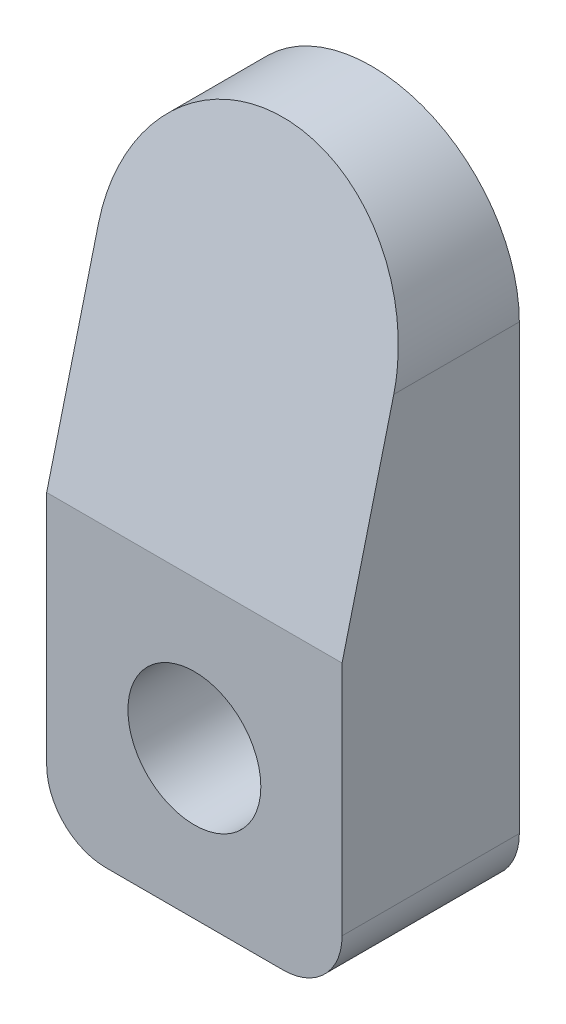
SolidWorks part; units mm, degrees
ref_plane "Front Plane" through (0, 0, 0) normal (0, 0, 1) x (1, 0, 0)
ref_plane "Top Plane" through (0, 0, 0) normal (0, 1, 0) x (1, 0, 0)
ref_plane "Right Plane" through (0, 0, 0) normal (1, 0, 0) x (0, 0, -1)
sketch "Sketch1" plane through (0, 0, 0) normal (0, 0, 1) x (1, 0, 0)
  line L2 (-5, 12) -> (-5, -5)
  line L3 (-5, -5) -> (5, -5)
  line L4 (5, 12) -> (5, -5)
  circle A0 centre (0, 0) radius 2.25
  arc A1 (5, 12) -> (-5, 12) centre (0, 12) ccw
  dimension "D4" = 4.5
  dimension "D1" = 12
  dimension "D2" = 5
  dimension "D3" = 10
extrude "Boss-Extrude1" add sketch "Sketch1" along normal blind 6
sketch "Sketch2" plane through (5, 0, 0) normal (1, 0, 0) x (0, 0, -1)
  line L0 (-6, 5) -> (-3, 17)
  line L1 (-6, -5) -> (-6, 12) construction
  line L3 (-3, 17) -> (-6, 17)
  line L4 (-6, 17) -> (-6, 5)
  line L5 (-6, -5) -> (0, -5) construction
  line L6 (0, 12) -> (0, 17) construction
  dimension "D1" = 10
  dimension "D2" = 3
extrude "Cut-Extrude1" cut sketch "Sketch2" against normal through all
fillet "Fillet1" radius 2 2 edges at (-5, -5, 3) (5, -5, 3)
